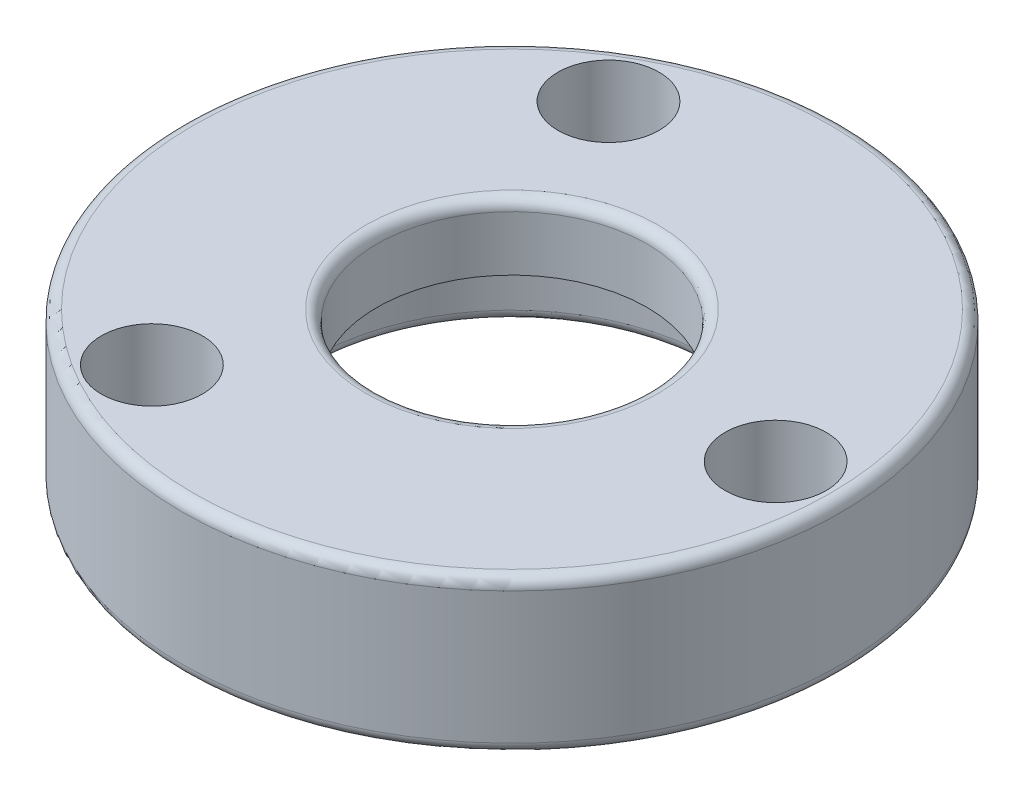
SolidWorks part; units mm, degrees
ref_plane "Front Plane" through (0, 0, 0) normal (0, 0, 1) x (1, 0, 0)
ref_plane "Top Plane" through (0, 0, 0) normal (0, 1, 0) x (1, 0, 0)
ref_plane "Right Plane" through (0, 0, 0) normal (1, 0, 0) x (0, 0, -1)
sketch "Sketch1" plane through (0, 0, 0) normal (0, 0, 1) x (1, 0, 0)
  line L0 (0, 0) -> (0, 9.384) construction
  line L1 (-4.572, 0) -> (-7.5, 0)
  line L2 (-7.5, 0) -> (-7.5, 3.5)
  line L3 (-7.5, 3.5) -> (-3.0734, 3.5)
  line L4 (-3.0734, 3.5) -> (-3.0734, 2)
  line L5 (-3.0734, 2) -> (-4.572, 2)
  line L6 (-4.572, 2) -> (-4.572, 0)
  dimension "D1" = 6.1468
  dimension "D2" = 9.144
  dimension "D3" = 2
  dimension "D4" = 1.5
  dimension "D5" = 15
revolve "Revolve1" add sketch "Sketch1" angle 360 about L0
sketch "Sketch2" plane through (0, 3.5, 0) normal (0, 1, 0) x (1, 0, 0)
  line L0 (0, 0) -> (6, 0) construction
  line L1 (0, 0) -> (-3, 5.1962) construction
  line L2 (0, 0) -> (-3, -5.1962) construction
  circle A0 centre (0, 0) radius 6 construction
  circle A1 centre (6, 0) radius 1.15
  circle A2 centre (-3, -5.1962) radius 1.15
  circle A3 centre (-3, 5.1962) radius 1.15
  dimension "D1" = 12
  dimension "D4" = 2.3
  dimension "D2" = 120
  dimension "D3" = 120
extrude "Cut-Extrude1" cut sketch "Sketch2" against normal blind 10
fillet "Fillet3" radius 0.25 1 edges at (0, 3.5, -3.0734)
fillet "Fillet4" radius 0.25 1 edges at (0, 3.5, -7.5)
fillet "Fillet5" radius 0.25 2 edges at (0, 0, -4.572) (0, 0, -7.5)
